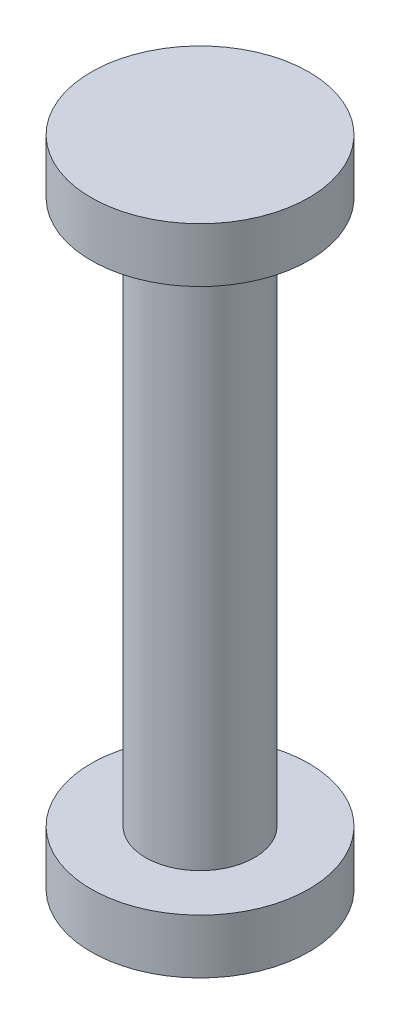
SolidWorks part; units mm, degrees
ref_plane "Front Plane" through (0, 0, 0) normal (0, 0, 1) x (1, 0, 0)
ref_plane "Top Plane" through (0, 0, 0) normal (0, 1, 0) x (1, 0, 0)
ref_plane "Right Plane" through (0, 0, 0) normal (1, 0, 0) x (0, 0, -1)
sketch "Sketch1" plane through (0, 0, 0) normal (0, 1, 0) x (1, 0, 0)
  circle A0 centre (0, 0) radius 5
  dimension "D1" = 10
extrude "Boss-Extrude1" add sketch "Sketch1" along normal mid plane 50
sketch "Sketch2" plane through (0, -25, 0) normal (0, -1, 0) x (1, 0, 0)
  circle A0 centre (0, 0) radius 10
  dimension "D1" = 20
extrude "Boss-Extrude3" add sketch "Sketch2" along normal blind 5
mirror "Mirror1" about plane through (0, 0, 0) normal (0, 1, 0) of "Boss-Extrude3"
